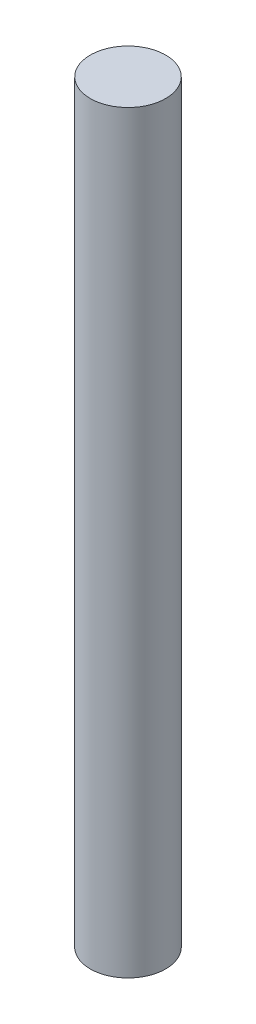
SolidWorks part; units mm, degrees
ref_plane "Front Plane" through (0, 0, 0) normal (0, 0, 1) x (1, 0, 0)
ref_plane "Top Plane" through (0, 0, 0) normal (0, 1, 0) x (1, 0, 0)
ref_plane "Right Plane" through (0, 0, 0) normal (1, 0, 0) x (0, 0, -1)
sketch "Sketch1" plane through (0, 0, 0) normal (0, 1, 0) x (1, 0, 0)
  circle A0 centre (0, 0) radius 4
  dimension "D1" = 8
extrude "Boss-Extrude1" add sketch "Sketch1" along normal blind 80
cosmetic thread "Cosmetic Thread1" parameters "D2"=6.619
